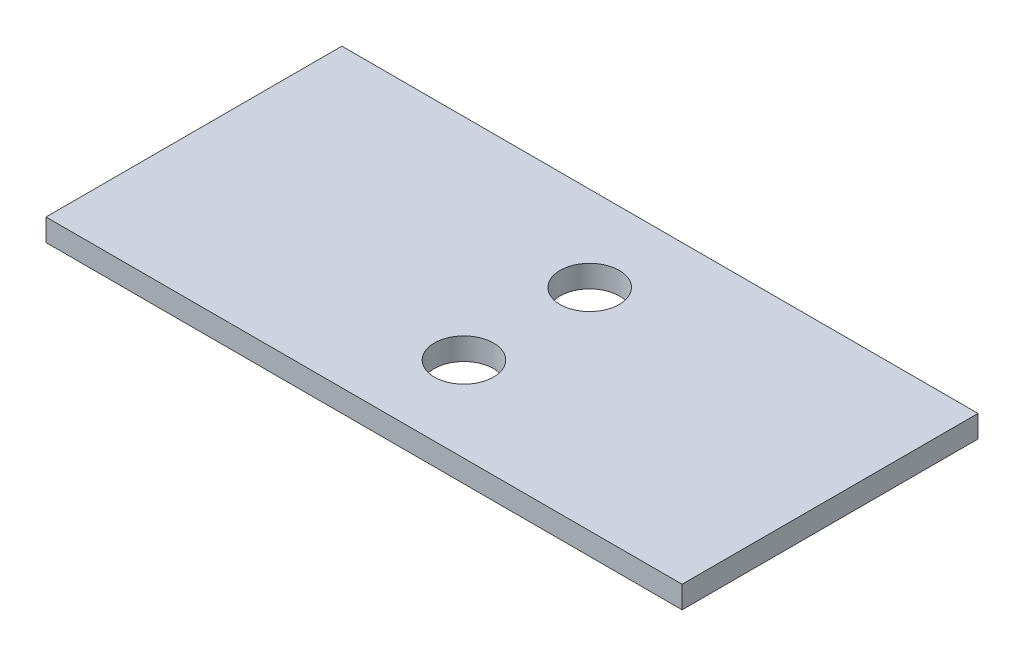
SolidWorks part; units mm, degrees
ref_plane "Спереди" through (0, 0, 0) normal (0, 0, 1) x (1, 0, 0)
ref_plane "Сверху" through (0, 0, 0) normal (0, 1, 0) x (1, 0, 0)
ref_plane "Справа" through (0, 0, 0) normal (1, 0, 0) x (0, 0, -1)
sketch "Эскиз1" plane through (0, 0, 0) normal (0, 1, 0) x (1, 0, 0)
  line L0 (22.5, 27.5782) -> (22.5, -2.9839) construction
  line L1 (0, 0) -> (43, 0)
  line L2 (0, 0) -> (0, 20)
  line L3 (0, 20) -> (43, 20)
  line L4 (43, 0) -> (43, 20)
  line L5 (0, 10) -> (43, 10) construction
  circle A0 centre (22.5, 14.25) radius 2
  circle A1 centre (22.5, 5.75) radius 2
extrude "Бобышка-Вытянуть1" add sketch "Эскиз1" along normal blind 1.5
